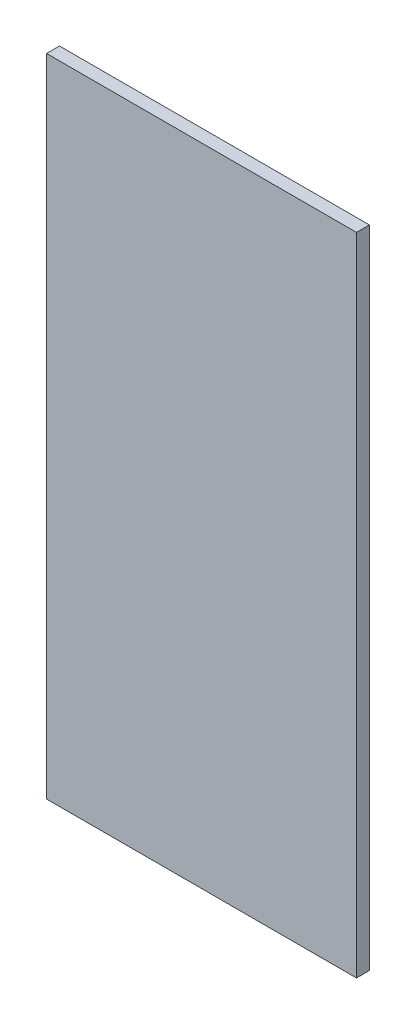
SolidWorks part; units mm, degrees
ref_plane "Alzado" through (0, 0, 0) normal (0, 0, 1) x (1, 0, 0)
ref_plane "Planta" through (0, 0, 0) normal (0, 1, 0) x (1, 0, 0)
ref_plane "Vista lateral" through (0, 0, 0) normal (1, 0, 0) x (0, 0, -1)
sketch "Croquis2" plane through (0, 0, 0) normal (0, 0, 1) x (1, 0, 0)
  line L1 (-76.2, 158.75) -> (76.2, 158.75)
  line L2 (-76.2, 158.75) -> (-76.2, -158.75)
  line L3 (-76.2, -158.75) -> (76.2, -158.75)
  line L4 (76.2, 158.75) -> (76.2, -158.75)
  line L5 (-76.2, 158.75) -> (76.2, -158.75) construction
  line L6 (-76.2, -158.75) -> (76.2, 158.75) construction
  point P0 (0, 0)
  dimension "D1" = 317.5
  dimension "D2" = 152.4
extrude "Saliente-Extruir1" add sketch "Croquis2" along normal blind 6.35
